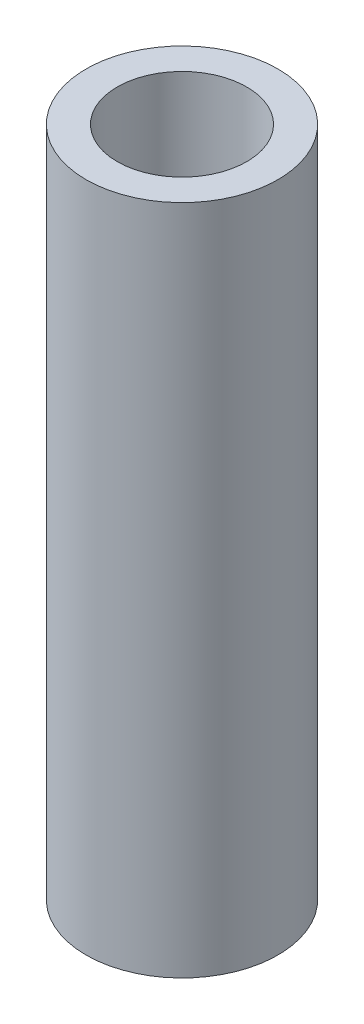
SolidWorks part; units mm, degrees
ref_plane "Front Plane" through (0, 0, 0) normal (0, 0, 1) x (1, 0, 0)
ref_plane "Top Plane" through (0, 0, 0) normal (0, 1, 0) x (1, 0, 0)
ref_plane "Right Plane" through (0, 0, 0) normal (1, 0, 0) x (0, 0, -1)
sketch "Sketch1" plane through (0, 0, 0) normal (0, 1, 0) x (1, 0, 0)
  circle A0 centre (0, 0) radius 1.7145
  circle A1 centre (0, 0) radius 2.54
  dimension "D1" = 3.429
  dimension "D2" = 5.08
extrude "Boss-Extrude1" add sketch "Sketch1" along normal blind 17.78
